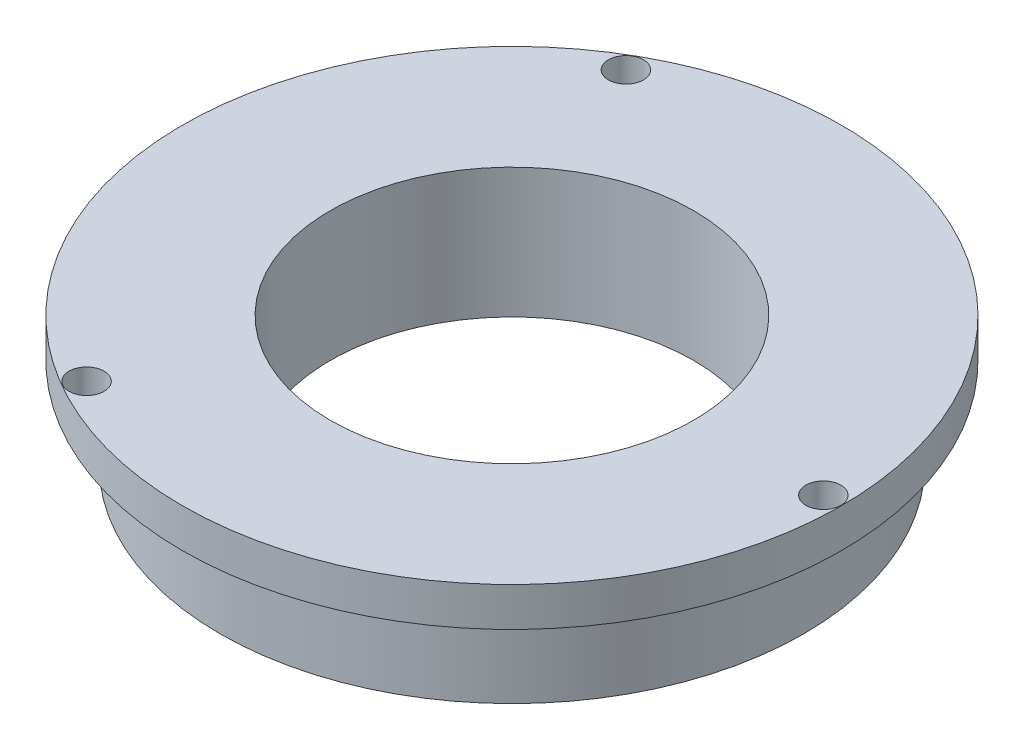
SolidWorks part; units mm, degrees
ref_plane "Alzado" through (0, 0, 0) normal (0, 0, 1) x (1, 0, 0)
ref_plane "Planta" through (0, 0, 0) normal (0, 1, 0) x (1, 0, 0)
ref_plane "Vista lateral" through (0, 0, 0) normal (1, 0, 0) x (0, 0, -1)
sketch "Croquis1" plane through (0, 0, 0) normal (0, 1, 0) x (1, 0, 0)
  circle A0 centre (0, 0) radius 25.4
  dimension "D1" = 50.8
extrude "Saliente-Extruir2" add sketch "Croquis1" along normal blind 10
sketch "Croquis4" plane through (0, 0, 0) normal (0, 1, 0) x (1, 0, 0)
  circle A0 centre (0, 0) radius 14
  dimension "D1" = 28
extrude "Cortar-Extruir2" cut sketch "Croquis4" along normal blind 47
sketch "Croquis5" plane through (0, 0, 0) normal (0, 1, 0) x (1, 0, 0)
  circle A0 centre (0, 0) radius 22.5
  circle A1 centre (0, 0) radius 25.4
  dimension "D1" = 45
extrude "Cortar-Extruir4" cut sketch "Croquis5" along normal blind 7
sketch "Croquis6" plane through (0, 0, 0) normal (0, 1, 0) x (1, 0, 0)
  circle A1 centre (24, 0) radius 1.35
  circle A2 centre (-12, -20.7846) radius 1.35
  circle A3 centre (-12, 20.7846) radius 1.35
  point P12 (0, 0)
  dimension "D2" = 2.7
  dimension "D3" = 3
extrude "Cortar-Extruir5" cut sketch "Croquis6" along normal blind 37
